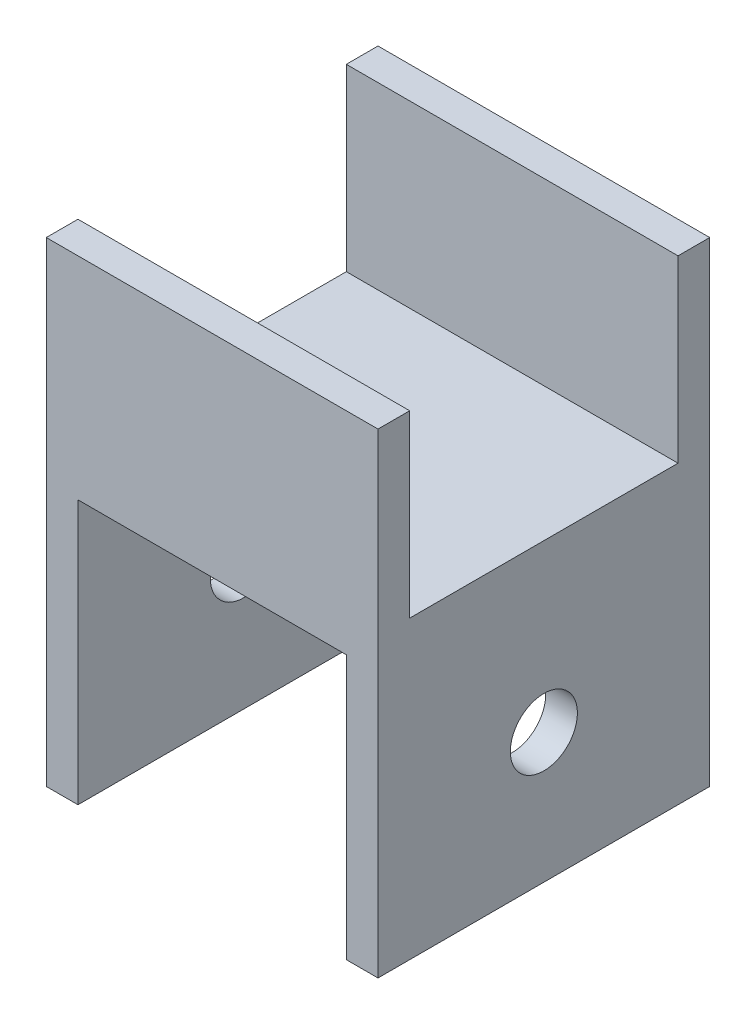
SolidWorks part; units mm, degrees
ref_plane "Front Plane" through (0, 0, 0) normal (0, 0, 1) x (1, 0, 0)
ref_plane "Top Plane" through (0, 0, 0) normal (0, 1, 0) x (1, 0, 0)
ref_plane "Right Plane" through (0, 0, 0) normal (1, 0, 0) x (0, 0, -1)
sketch "Sketch1" plane through (0, 0, 0) normal (1, 0, 0) x (0, 0, -1)
  line L0 (0, 0) -> (0, 20)
  line L1 (0, 20) -> (3, 20)
  line L5 (28.4, 20) -> (31.4, 20)
  line L6 (31.4, 20) -> (31.4, 0)
  line L7 (31.4, 0) -> (0, 0)
  line L8 (28.4, 20) -> (28.4, 3)
  line L13 (28.4, 3) -> (3, 3)
  line L14 (3, 3) -> (3, 20)
  dimension "D1" = 3
  dimension "D2" = 20
  dimension "D3" = 25.4
extrude "Boss-Extrude1" add sketch "Sketch1" along normal blind 31.4
sketch "Sketch2" plane through (0, 0, 0) normal (0, -1, 0) x (1, 0, 0)
  line L5 (31.4, -31.4) -> (0, -31.4) construction
  line L10 (31.4, 0) -> (28.4, 0)
  line L11 (31.4, 0) -> (31.4, -31.4)
  line L12 (31.4, -31.4) -> (28.4, -31.4)
  line L13 (28.4, 0) -> (28.4, -31.4)
  line L14 (31.4, 0) -> (0, 0) construction
  line L15 (0, -31.4) -> (3, -31.4)
  line L16 (0, -31.4) -> (0, 0)
  line L17 (0, 0) -> (3, 0)
  line L18 (3, -31.4) -> (3, 0)
  dimension "D1" = 3
  dimension "D2" = 3
extrude "Boss-Extrude2" add sketch "Sketch2" along normal blind 25
sketch "Sketch4" plane through (0, 0, 0) normal (0, 0, 1) x (1, 0, 0)
  line L0 (31.4, 20) -> (0, 20) construction
  circle A0 centre (15.7, 11) radius 1.5
  point P6 (15.7, 20)
  dimension "D1" = 3
  dimension "D2" = 9
extrude "Cut-Extrude2" [suppressed] cut sketch "Sketch4" against normal through all both and the other way through all
hole_wizard "1/4 (0.25) Diameter Hole1" positions "Sketch5" profile "Sketch6" hole size "1/4" standard "ANSI Inch" end condition through all
sketch "Sketch5" plane through (31.4, 0, 0) normal (1, 0, 0) x (0, 0, -1)
  line L1 (28.4, 3) -> (3, 3) construction
  point P0 (15.7, -12.7)
  point P8 (15.7, 3)
  dimension "D1" = 12.7
sketch "Sketch6" plane through (31.4, -12.7, -15.7) normal (0, 1, 0) x (0, 0, -1)
  line L0 (0, 0) -> (0, 31.4)
  line L1 (0, 31.4) -> (3.175, 31.4)
  line L2 (3.175, 31.4) -> (3.175, 0)
  line L5 (3.175, 0) -> (0, 0)
  line L11 (0, -6.35) -> (0, 107.95) construction
  dimension "Thru Hole Dia." = 6.35
  dimension "Thru Hole Depth" = 31.4
